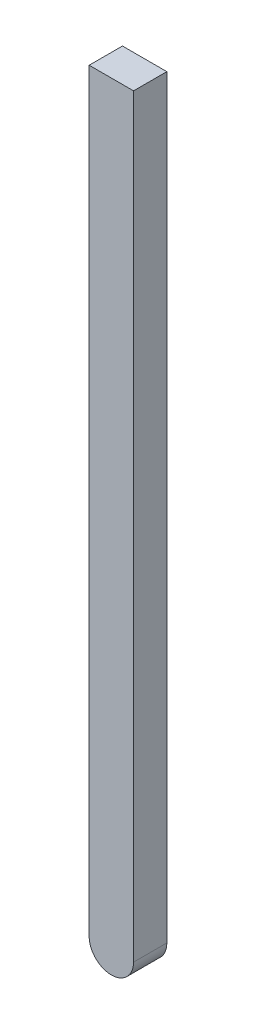
SolidWorks part; units mm, degrees
ref_plane "Płaszczyzna przednia" through (0, 0, 0) normal (0, 0, 1) x (1, 0, 0)
ref_plane "Płaszczyzna górna" through (0, 0, 0) normal (0, 1, 0) x (1, 0, 0)
ref_plane "Płaszczyzna prawa" through (0, 0, 0) normal (1, 0, 0) x (0, 0, -1)
sketch "Szkic1" plane through (0, 0, 0) normal (0, 0, 1) x (1, 0, 0)
  line L1 (0, 0) -> (40, 0)
  line L2 (0, 0) -> (0, -680)
  line L4 (40, 0) -> (40, -680)
  arc A0 (0, -680) -> (40, -680) centre (20, -680) ccw
  dimension "D3" = 20
  dimension "D1" = 680
  dimension "D2" = 40
extrude "Dodanie-wyciągnięcie1" add sketch "Szkic1" along normal blind 30
